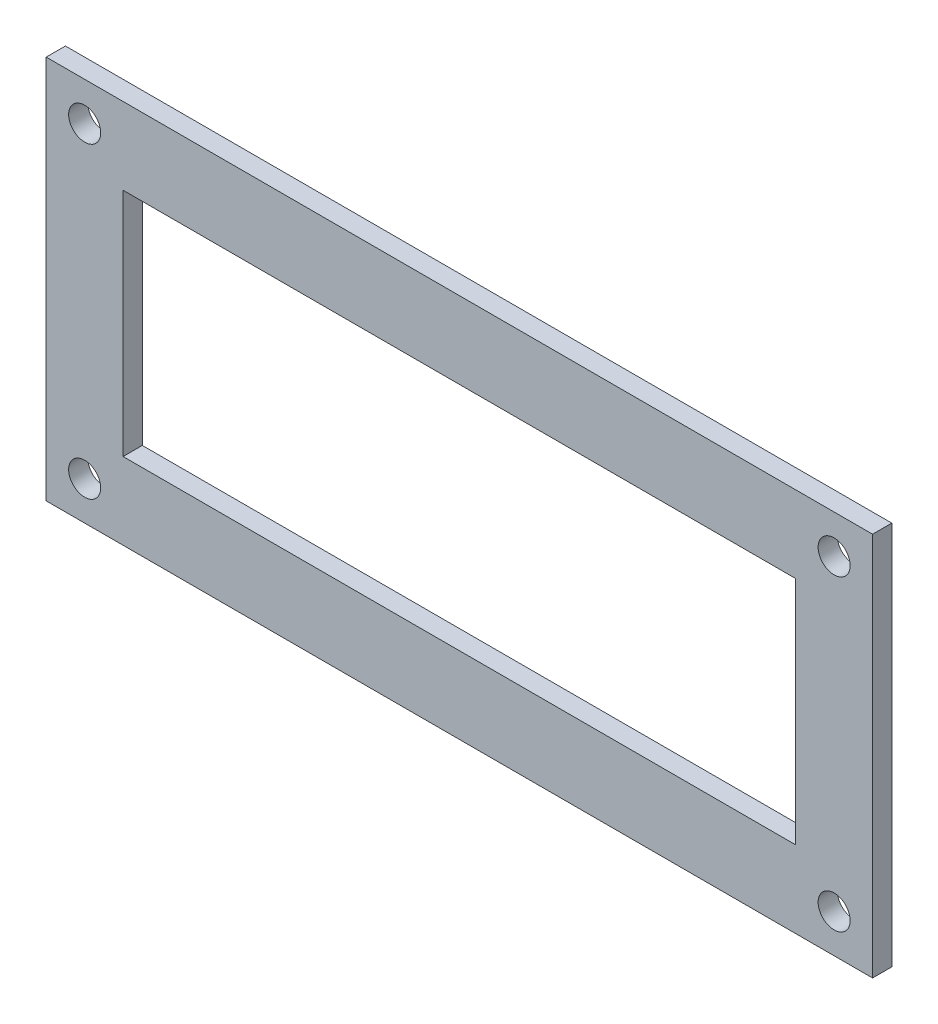
SolidWorks part; units mm, degrees
ref_plane "Front Plane" through (0, 0, 0) normal (0, 0, 1) x (1, 0, 0)
ref_plane "Top Plane" through (0, 0, 0) normal (0, 1, 0) x (1, 0, 0)
ref_plane "Right Plane" through (0, 0, 0) normal (1, 0, 0) x (0, 0, -1)
sketch "Sketch1" plane through (0, 0, 0) normal (0, 0, 1) x (1, 0, 0)
  line L1 (0, 0) -> (129, 0)
  line L2 (0, 0) -> (0, 60)
  line L3 (0, 60) -> (129, 60)
  line L4 (129, 0) -> (129, 60)
  line L5 (12, 48) -> (117, 48)
  line L6 (12, 48) -> (12, 12)
  line L7 (12, 12) -> (117, 12)
  line L8 (117, 48) -> (117, 12)
  circle A0 centre (6, 6) radius 2.5
  circle A1 centre (6, 54) radius 2.5
  circle A2 centre (123, 54) radius 2.5
  circle A3 centre (123, 6) radius 2.5
  dimension "D2" = 6
  dimension "D3" = 6
  dimension "D4" = 5
  dimension "D6" = 6
  dimension "D9" = 6
  dimension "D10" = 6
  dimension "D1" = 60
  dimension "D5" = 6
  dimension "D7" = 105
  dimension "D8" = 6
  dimension "D11" = 6
extrude "Boss-Extrude1" add sketch "Sketch1" along normal blind 3
